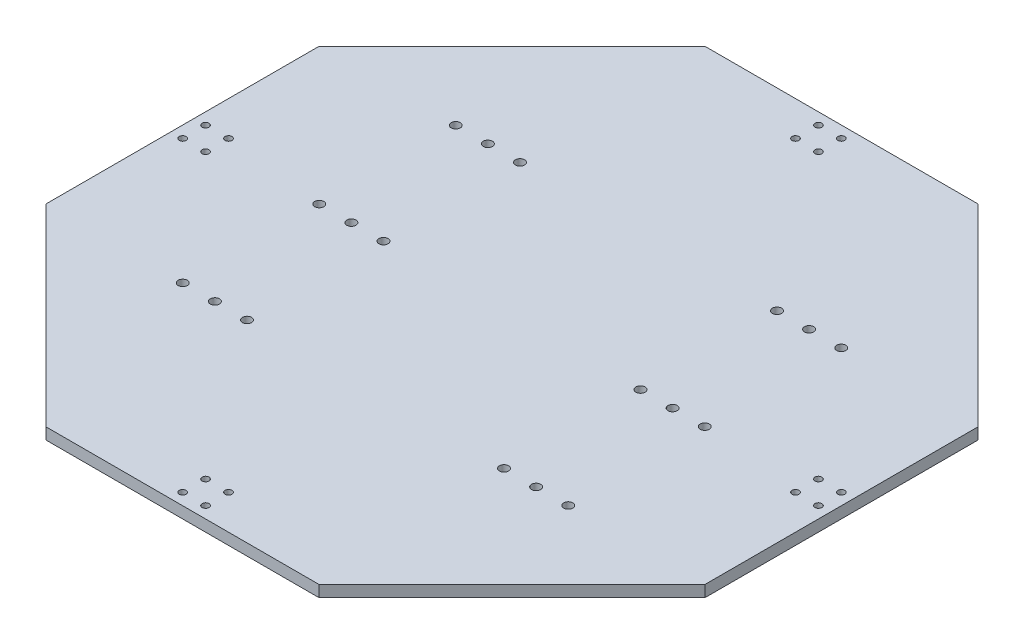
SolidWorks part; units mm, degrees
material "6061 합금"
ref_plane "정면" through (0, 0, 0) normal (0, 0, 1) x (1, 0, 0)
ref_plane "윗면" through (0, 0, 0) normal (0, 1, 0) x (1, 0, 0)
ref_plane "우측면" through (0, 0, 0) normal (1, 0, 0) x (0, 0, -1)
sketch "스케치1" plane through (0, 0, 0) normal (0, 1, 0) x (1, 0, 0)
  line L0 (0, 278.2405) -> (0, -303.6506) construction
  line L1 (-342.3832, 0) -> (358.9353, 0) construction
  line L3 (59.4811, -143.6) -> (143.6, -59.4811)
  line L4 (143.6, -59.4811) -> (143.6, 59.4811)
  line L5 (143.6, 59.4811) -> (59.4811, 143.6)
  line L6 (59.4811, 143.6) -> (-59.4811, 143.6)
  line L7 (-59.4811, 143.6) -> (-143.6, 59.4811)
  line L8 (-143.6, 59.4811) -> (-143.6, -59.4811)
  line L9 (-143.6, -59.4811) -> (-59.4811, -143.6)
  line L10 (-59.4811, -143.6) -> (59.4811, -143.6)
  circle A0 centre (0, 0) radius 143.6 construction
  circle A1 centre (-5, 138.54) radius 1.5
  circle A2 centre (-5, 128.54) radius 1.5
  circle A7 centre (5, 128.54) radius 1.5
  circle A8 centre (5, 138.54) radius 1.5
  circle A9 centre (138.54, 5) radius 1.5
  circle A10 centre (128.54, 5) radius 1.5
  circle A15 centre (128.54, -5) radius 1.5
  circle A16 centre (138.54, -5) radius 1.5
  circle A17 centre (5, -138.54) radius 1.5
  circle A18 centre (5, -128.54) radius 1.5
  circle A23 centre (-5, -128.54) radius 1.5
  circle A24 centre (-5, -138.54) radius 1.5
  circle A25 centre (-138.54, -5) radius 1.5
  circle A26 centre (-128.54, -5) radius 1.5
  circle A31 centre (-128.54, 5) radius 1.5
  circle A32 centre (-138.54, 5) radius 1.5
  point P82 (0, 0)
  point P115 (0, -46.8105)
  dimension "D2" = 3
  dimension "D5" = 3
  dimension "D1" = 287.2
  dimension "D3" = 5
  dimension "D4" = 5.06
  dimension "D6" = 10
  dimension "D11" = 4
extrude "보스-돌출1" add sketch "스케치1" along normal blind 5
ref_plane "평면1" through (0, 5, 0) normal (0, 1, 0) x (1, 0, 0)
sketch "스케치2" plane through (0, 5, 0) normal (0, 1, 0) x (1, 0, 0)
  line L0 (-143.6, 0) -> (143.6, 0) construction
  line L1 (-143.6, 59.4811) -> (-143.6, -59.4811) construction
  line L2 (143.6, -59.4811) -> (143.6, 59.4811) construction
  line L3 (-143.6, 59.4811) -> (143.6, 59.4811) construction
  line L4 (59.4811, 143.6) -> (-59.4811, 143.6) construction
  line L5 (0, 143.6) -> (0, -143.6) construction
  line L6 (-59.4811, -143.6) -> (59.4811, -143.6) construction
  line L7 (-143.6, 29.7411) -> (143.6, 29.7411) construction
  line L8 (-143.6, -59.4811) -> (143.6, -59.4811) construction
  line L9 (-143.6, -29.7411) -> (143.6, -29.7411) construction
  circle A0 centre (-56, 0) radius 2
  circle A1 centre (-56, 59.4821) radius 2
  circle A2 centre (-56, -59.4821) radius 2
  circle A3 centre (70, 0) radius 2
  circle A4 centre (70, 59.4821) radius 2
  circle A5 centre (70, -59.4821) radius 2
  circle A6 centre (-70, -59.4821) radius 2
  circle A7 centre (-70, 59.4821) radius 2
  circle A8 centre (-70, 0) radius 2
  circle A9 centre (56, -59.4821) radius 2
  circle A10 centre (56, 59.4821) radius 2
  circle A11 centre (56, 0) radius 2
  circle A12 centre (-84, 0) radius 2
  circle A13 centre (-84, 59.4821) radius 2
  circle A14 centre (-84, -59.4821) radius 2
  circle A15 centre (84, -59.4821) radius 2
  circle A16 centre (84, 59.4821) radius 2
  circle A17 centre (84, 0) radius 2
  point P6 (-58, 0)
  point P46 (-72, 0)
  point P50 (68, 0)
  point P51 (58, 0)
  point P60 (-82, 0)
  point P67 (82, 0)
  dimension "D3" = 4
  dimension "D2" = 14
  dimension "D1" = 14
  dimension "D4" = 29.74
  dimension "D5" = 56
extrude "컷-돌출1" cut sketch "스케치2" against normal blind 10
